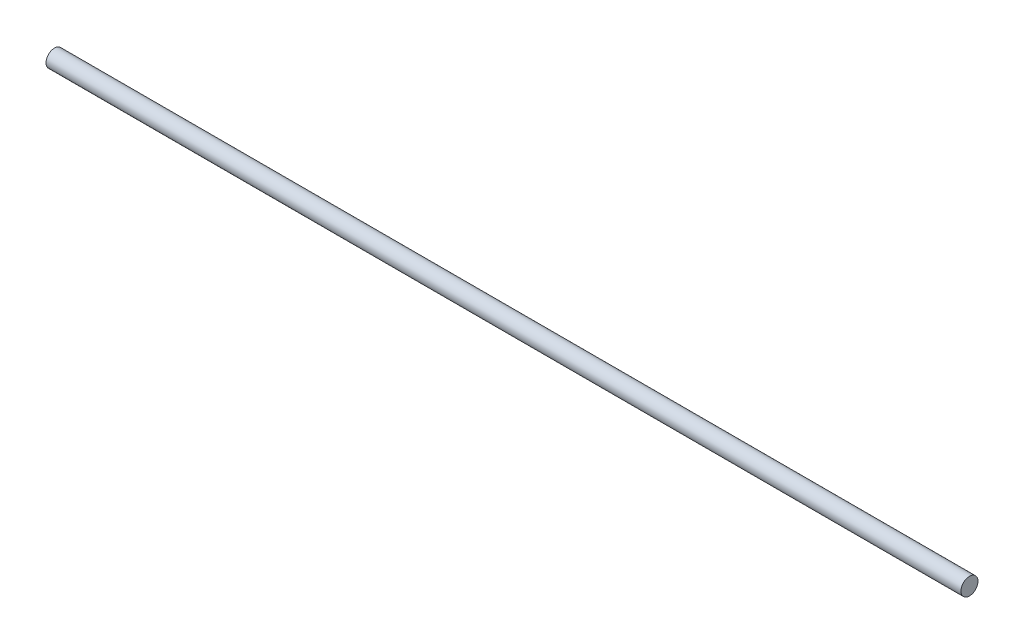
SolidWorks part; units mm, degrees
ref_plane "Front Plane" through (0, 0, 0) normal (0, 0, 1) x (1, 0, 0)
ref_plane "Top Plane" through (0, 0, 0) normal (0, 1, 0) x (1, 0, 0)
ref_plane "Right Plane" through (0, 0, 0) normal (1, 0, 0) x (0, 0, -1)
sketch "Sketch1" plane through (0, 0, 0) normal (1, 0, 0) x (0, 0, -1)
  circle A0 centre (0, 0) radius 0.003
  circle A1 centre (0, 0) radius 3
extrude "Boss-Extrude1" add sketch "Sketch1" along normal mid plane 322
